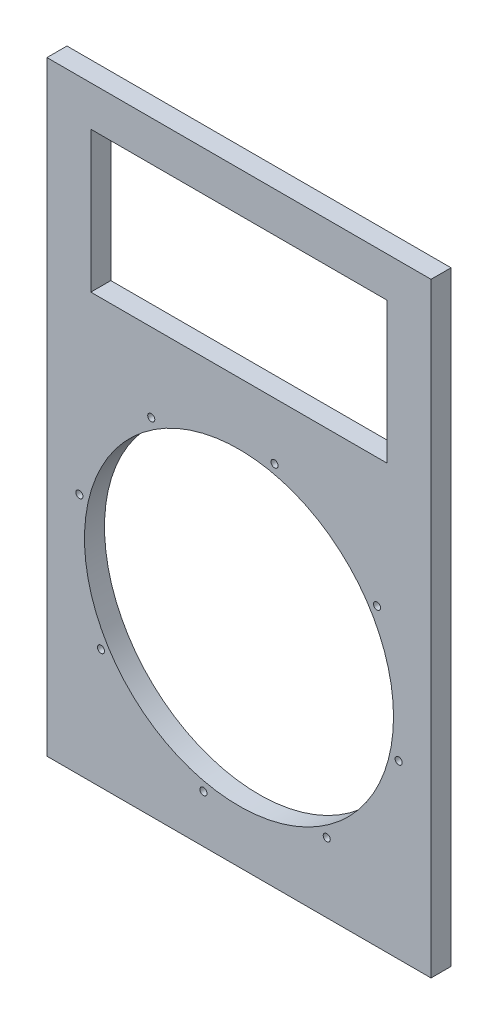
SolidWorks part; units mm, degrees
ref_plane "Front Plane" through (0, 0, 0) normal (0, 0, 1) x (1, 0, 0)
ref_plane "Top Plane" through (0, 0, 0) normal (0, 1, 0) x (1, 0, 0)
ref_plane "Right Plane" through (0, 0, 0) normal (1, 0, 0) x (0, 0, -1)
sketch "Sketch1" plane through (0, 0, 0) normal (0, 0, 1) x (1, 0, 0)
  line L1 (0, 0) -> (345.7, 0)
  line L2 (0, 0) -> (0, 544.6)
  line L3 (0, 544.6) -> (345.7, 544.6)
  line L4 (345.7, 0) -> (345.7, 544.6)
  dimension "D1" = 345.7
  dimension "D2" = 544.6
extrude "Boss-Extrude1" add sketch "Sketch1" along normal blind 18
sketch "Sketch2" plane through (0, 0, 18) normal (0, 0, 1) x (1, 0, 0)
  line L0 (0, 0) -> (345.7, 0) construction
  line L1 (39.5, 508.5) -> (306.2, 508.5)
  line L2 (39.5, 508.5) -> (39.5, 381.5)
  line L3 (39.5, 381.5) -> (306.2, 381.5)
  line L4 (306.2, 508.5) -> (306.2, 381.5)
  line L5 (345.7, 544.6) -> (0, 544.6) construction
  point P4 (306.2, 445)
  point P7 (172.85, 508.5)
  point P10 (172.85, 544.6)
  dimension "D1" = 445
  dimension "D2" = 127
  dimension "D3" = 266.7
  dimension "D4" = 0
extrude "Cut-Extrude1" cut sketch "Sketch2" against normal through all
sketch "Sketch3" plane through (0, 0, 18) normal (0, 0, 1) x (1, 0, 0)
  line L0 (39.5, 381.5) -> (306.2, 381.5) construction
  circle A0 centre (172.85, 186.691) radius 139.065
  point P4 (172.85, 381.5)
  dimension "D2" = 278.13
  dimension "D1" = 0
extrude "Cut-Extrude2" cut sketch "Sketch3" against normal through all
sketch "Sketch4" plane through (0, 0, 18) normal (0, 0, 1) x (1, 0, 0)
  circle A1 centre (204.8422, 330.3652) radius 3.175
  circle A2 centre (297.0649, 265.6621) radius 3.175
  circle A3 centre (316.5242, 154.6988) radius 3.175
  circle A4 centre (251.8211, 62.4761) radius 3.175
  circle A5 centre (140.8578, 43.0167) radius 3.175
  circle A6 centre (48.6351, 107.7198) radius 3.175
  circle A7 centre (29.1758, 218.6831) radius 3.175
  circle A8 centre (93.8789, 310.9059) radius 3.175
  point P20 (172.85, 186.691)
  dimension "D2" = 6.35
  dimension "D3" = 8
extrude "Cut-Extrude3" cut sketch "Sketch4" against normal through all
